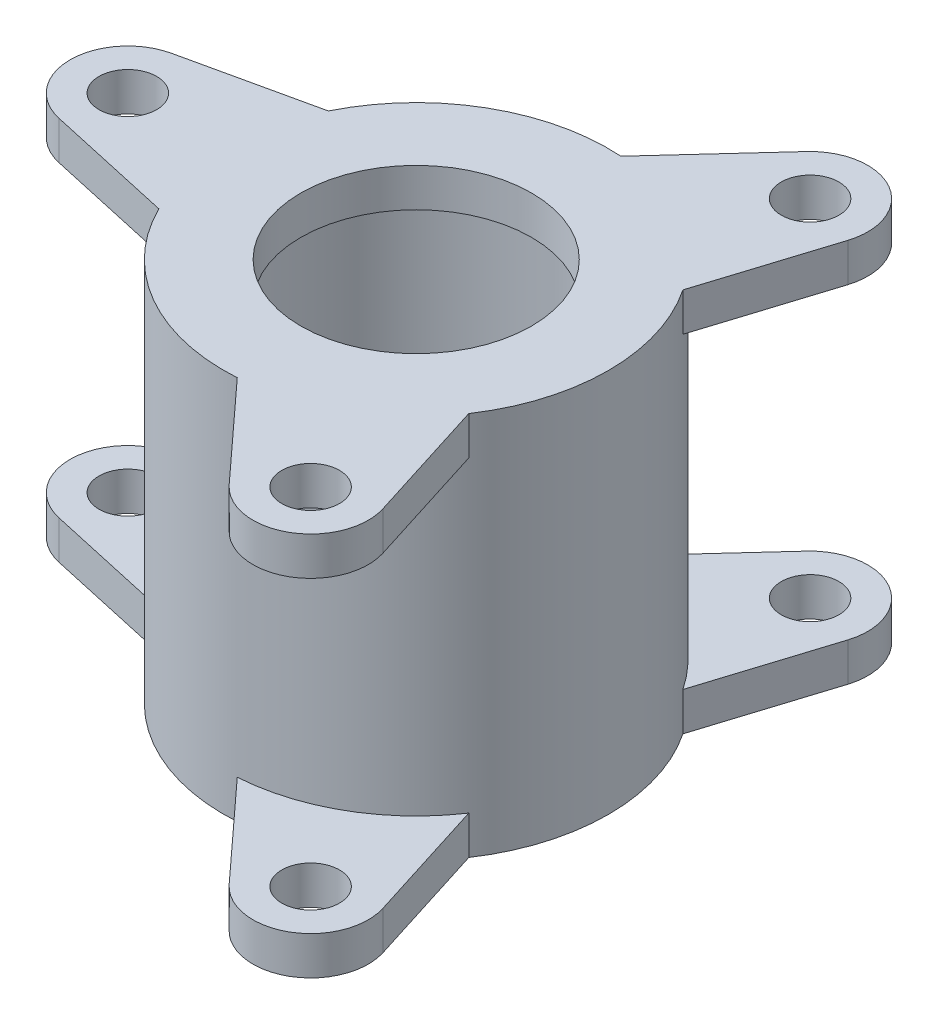
SolidWorks part; units mm, degrees
ref_plane "Front Plane" through (0, 0, 0) normal (0, 0, 1) x (1, 0, 0)
ref_plane "Top Plane" through (0, 0, 0) normal (0, 1, 0) x (1, 0, 0)
ref_plane "Right Plane" through (0, 0, 0) normal (1, 0, 0) x (0, 0, -1)
sketch "Sketch1" plane through (0, 0, 0) normal (0, 0, 1) x (1, 0, 0)
  line L0 (0, 0) -> (0, 68.2451) construction
  line L1 (35, 0) -> (35, 5)
  line L2 (35, 5) -> (40, 5)
  line L3 (40, 5) -> (40, 90)
  line L4 (40, 90) -> (30, 90)
  line L5 (30, 90) -> (30, 100)
  line L6 (30, 100) -> (50, 100)
  line L8 (50, 0) -> (35, 0)
  line L9 (50, 100) -> (50, 0)
  dimension "D1" = 80
  dimension "D2" = 70
  dimension "D3" = 60
  dimension "D4" = 100
  dimension "D5" = 10
  dimension "D6" = 5
  dimension "D7" = 100
revolve "Revolve1" add sketch "Sketch1" angle 360 about L0
sketch "Sketch2" plane through (0, 100, 0) normal (0, 1, 0) x (1, 0, 0)
  line L0 (-78.2466, 14.6444) -> (-44.8794, 22.0418)
  line L1 (-78.2466, -14.6444) -> (-44.8794, -22.0418)
  circle A0 centre (0, 0) radius 75 construction
  arc A1 (-78.2466, 14.6444) -> (-78.2466, -14.6444) centre (-75, 0) ccw
  circle A2 centre (-75, 0) radius 7.5
  circle A3 centre (0, 0) radius 50 construction
  arc A4 (-44.8794, 22.0418) -> (-44.8794, -22.0418) centre (0, 0) ccw
  dimension "D1" = 150
  dimension "D2" = 15
  dimension "D3" = 30
  dimension "D4" = 25
extrude "Boss-Extrude1" add sketch "Sketch2" against normal blind 10
pattern_circular "CirPattern1" count 3 over 360 about axis through (0, 0, 0) along (0, 1, 0) of "Boss-Extrude1"
ref_plane "Plane1" through (0, 50, 0) normal (0, 1, 0) x (1, 0, 0)
mirror "Mirror1" about plane through (0, 50, 0) normal (0, 1, 0) of "CirPattern1", "Boss-Extrude1"
